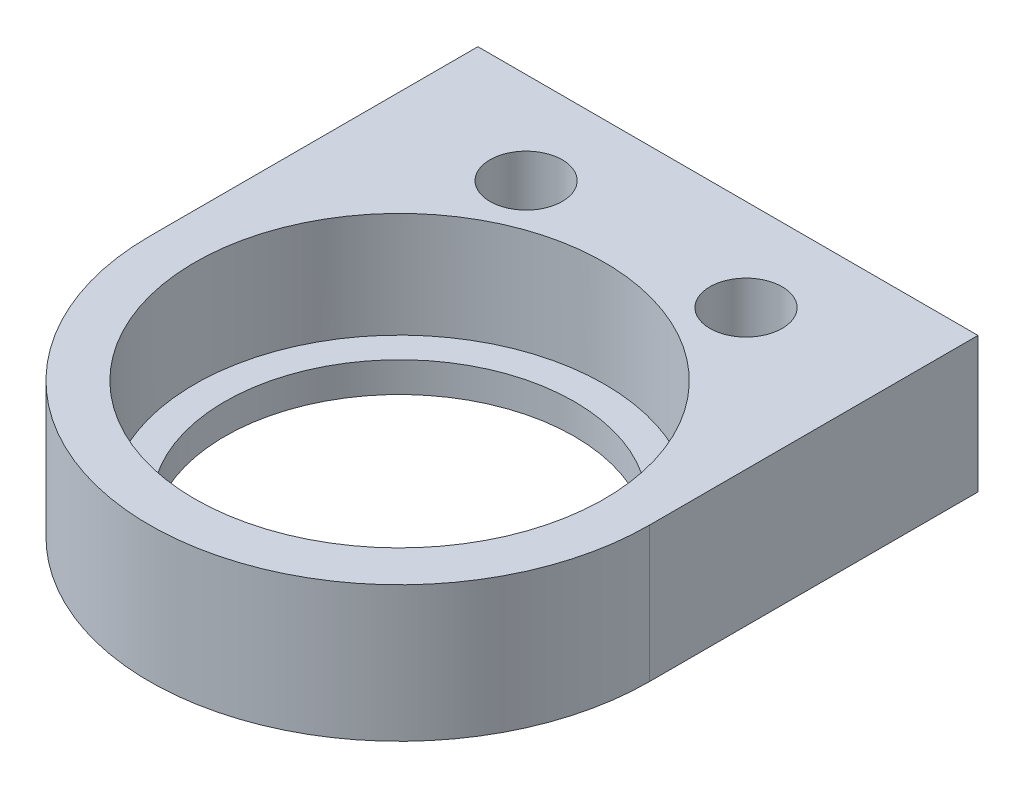
SolidWorks part; units mm, degrees
ref_plane "Front Plane" through (0, 0, 0) normal (0, 0, 1) x (1, 0, 0)
ref_plane "Top Plane" through (0, 0, 0) normal (0, 1, 0) x (1, 0, 0)
ref_plane "Right Plane" through (0, 0, 0) normal (1, 0, 0) x (0, 0, -1)
sketch "Sketch1" plane through (0, 0, 0) normal (0, 1, 0) x (1, 0, 0)
  line L0 (0, 0) -> (14.2506, 0) construction
  line L1 (0, 0) -> (0, 17.6258) construction
  line L3 (-7.366, 0) -> (-7.366, 13.843) construction
  line L4 (-10.541, 0) -> (-10.541, 10.668)
  line L5 (-10.541, 10.668) -> (-20.066, 10.668)
  line L6 (-7.366, 13.843) -> (-20.066, 13.843)
  line L7 (-20.066, 10.668) -> (-20.066, 13.843)
  line L9 (-7.366, 13.843) -> (7.366, 13.843)
  line L11 (10.541, 0) -> (10.541, 10.668)
  line L12 (20.066, 10.668) -> (20.066, 13.843)
  line L13 (7.366, 13.843) -> (20.066, 13.843)
  line L14 (10.541, 10.668) -> (20.066, 10.668)
  line L17 (-7.366, 6.9215) -> (-7.366, 10.668) construction
  line L18 (7.366, 6.9215) -> (7.366, 10.668) construction
  line L19 (-7.366, 10.668) -> (7.366, 10.668) construction
  circle A0 centre (0, 0) radius 6.096
  circle A1 centre (0, 0) radius 10.541 construction
  arc A3 (10.541, 0) -> (-10.541, 0) centre (0, 0) cw
  arc A5 (-7.366, 6.9215) -> (7.366, 6.9215) centre (0, 0) cw construction
  point P18 (0, 13.843)
  point P19 (0, 10.668)
  dimension "D1" = 12.192
  dimension "D2" = 4.445
  dimension "D3" = 13.843
  dimension "D4" = 3.175
  dimension "D5" = 12.7
extrude "Boss-Extrude1" add sketch "Sketch1" along normal blind 4.445
sketch "Sketch5" plane through (0, 0, 0) normal (0, -1, 0) x (1, 0, 0)
  line L0 (-10.541, 0) -> (-10.541, -10.668)
  line L6 (10.541, -10.668) -> (10.541, 0)
  line L7 (-10.541, -10.668) -> (-10.541, -13.843)
  line L9 (20.066, -13.843) -> (-20.066, -13.843) construction
  line L10 (-10.541, -13.843) -> (10.541, -13.843)
  line L12 (10.541, -10.668) -> (10.541, -13.843)
  circle A1 centre (0, 0) radius 6.096 construction
  circle A2 centre (0, 0) radius 9.271 construction
  circle A3 centre (0, 0) radius 7.366
  arc A4 (10.541, 0) -> (-10.541, 0) centre (0, 0) ccw
  dimension "D1" = 14.732
extrude "Boss-Extrude4" add sketch "Sketch5" along normal blind 1.27
sketch "Sketch8" plane through (0, 4.445, 0) normal (0, 1, 0) x (1, 0, 0)
  circle A0 centre (0, 0) radius 8.636
  dimension "D1" = 17.272
extrude "Cut-Extrude4" cut sketch "Sketch8" against normal up to surface (4.445 mm away) up to face at (0, 0, 6.096)
sketch "Sketch6" plane through (0, 4.445, 0) normal (0, 1, 0) x (1, 0, 0)
  line L0 (0, 13.843) -> (0, 9.9695) construction
  line L2 (0, 9.9695) -> (10.541, 9.9695) construction
  line L3 (10.541, 0) -> (10.541, 10.668) construction
  line L4 (20.066, 13.843) -> (-20.066, 13.843) construction
  circle A1 centre (4.6355, 9.9695) radius 1.524
  circle A2 centre (-4.6355, 9.9695) radius 1.524
  dimension "D1" = 3.048
  dimension "D2" = 4.6355
  dimension "D3" = 3.048
extrude "Cut-Extrude2" cut sketch "Sketch6" against normal through all
sketch "Sketch7" plane through (0, 0, -10.668) normal (0, 0, 1) x (1, 0, 0)
  line L1 (10.541, 0) -> (20.066, 0)
  line L2 (10.541, 0) -> (10.541, 4.445)
  line L3 (10.541, 4.445) -> (20.066, 4.445)
  line L4 (20.066, 0) -> (20.066, 4.445)
  line L5 (-10.541, 0) -> (-20.066, 0)
  line L6 (-10.541, 0) -> (-10.541, 4.445)
  line L7 (-10.541, 4.445) -> (-20.066, 4.445)
  line L8 (-20.066, 0) -> (-20.066, 4.445)
extrude "Cut-Extrude3" cut sketch "Sketch7" against normal up to surface (3.175 mm away) up to face at (0, 0.7937, -13.843)
